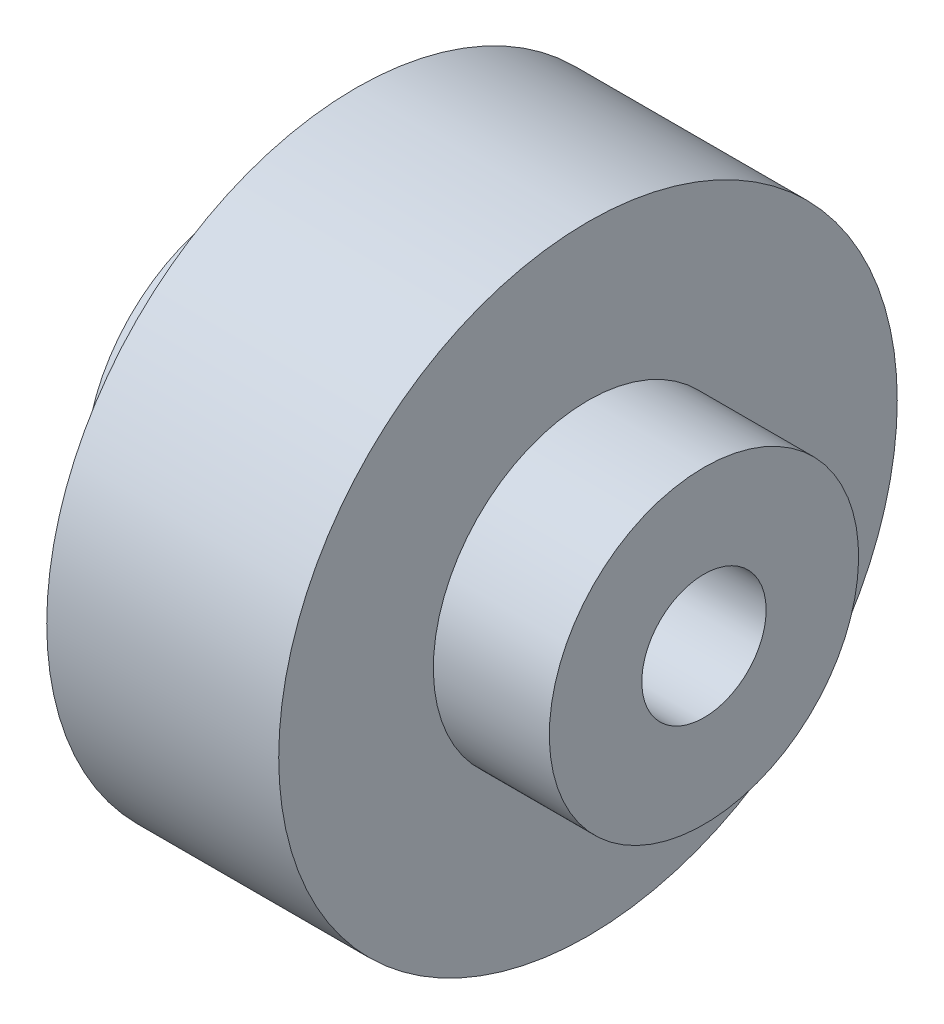
SolidWorks part; units mm, degrees
ref_plane "Front Plane" through (0, 0, 0) normal (0, 0, 1) x (1, 0, 0)
ref_plane "Top Plane" through (0, 0, 0) normal (0, 1, 0) x (1, 0, 0)
ref_plane "Right Plane" through (0, 0, 0) normal (1, 0, 0) x (0, 0, -1)
sketch "Sketch1" plane through (0, 0, 0) normal (0, 0, 1) x (1, 0, 0)
  line L0 (0, 0) -> (0, 6.35)
  line L1 (0, 6.35) -> (4.7625, 6.35)
  line L2 (4.7625, 6.35) -> (4.7625, 12.7)
  line L3 (4.7625, 12.7) -> (14.2875, 12.7)
  line L4 (14.2875, 12.7) -> (14.2875, 6.35)
  line L5 (14.2875, 6.35) -> (19.05, 6.35)
  line L6 (19.05, 6.35) -> (19.05, 0)
  line L7 (19.05, 0) -> (0, 0)
  dimension "D1" = 6.35
  dimension "D2" = 19.05
  dimension "D3" = 9.525
  dimension "D4" = 12.7
revolve "Revolve1" add sketch "Sketch1" angle 360 about L7
hole_wizard "1/4-20 Tapped Hole1" positions "Sketch2" profile "Sketch3" tap size "1/4-20" standard "ANSI Inch" end condition through all
sketch "Sketch2" plane through (19.05, 0, 0) normal (1, 0, 0) x (0, 0, -1)
  point P0 (0, 0)
sketch "Sketch3" plane through (19.05, 0, 0) normal (0, 1, 0) x (0, 0, -1)
  line L0 (0, 0) -> (0, 19.05)
  line L1 (0, 19.05) -> (2.5527, 19.05)
  line L2 (2.5527, 19.05) -> (2.5527, 0)
  line L5 (2.5527, 0) -> (0, 0)
  line L11 (0, -6.35) -> (0, 107.95) construction
  dimension "Thru Tap Drill Dia." = 5.1054
  dimension "Thru Tap Drill Depth" = 19.05
cosmetic thread "Hole Thread1"
